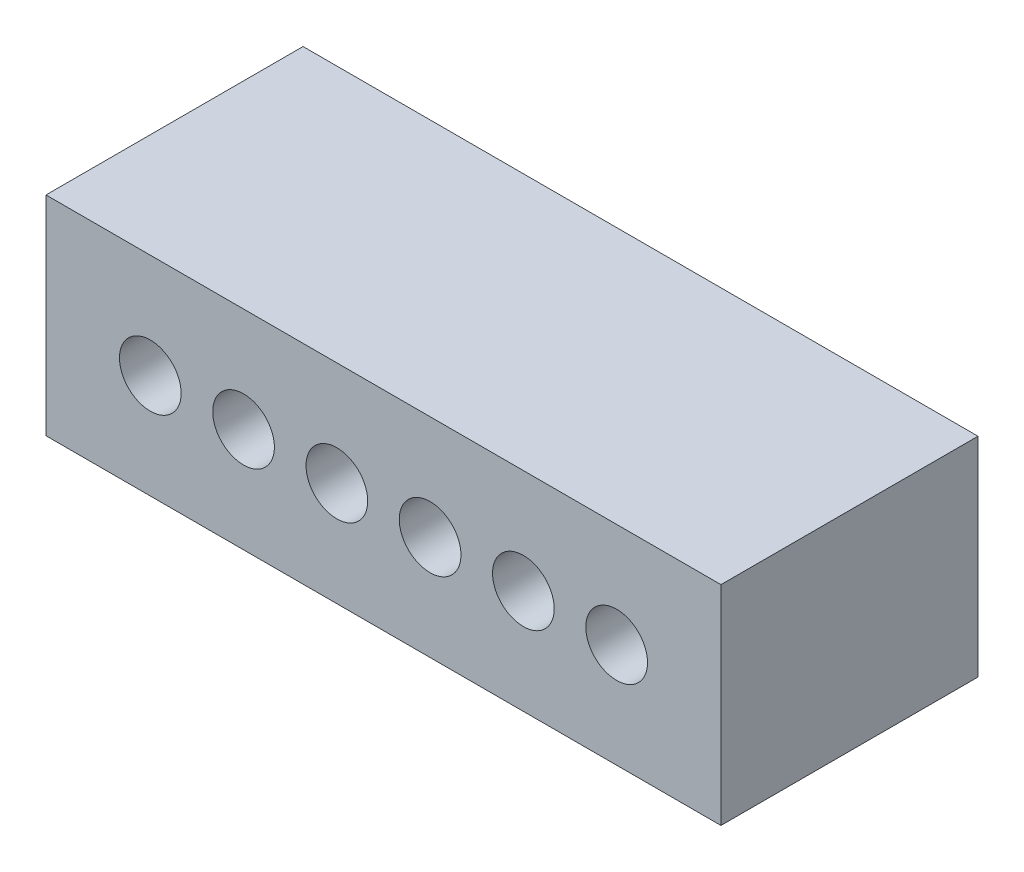
SolidWorks part; units mm, degrees
ref_plane "Front Plane" through (0, 0, 0) normal (0, 0, 1) x (1, 0, 0)
ref_plane "Top Plane" through (0, 0, 0) normal (0, 1, 0) x (1, 0, 0)
ref_plane "Right Plane" through (0, 0, 0) normal (1, 0, 0) x (0, 0, -1)
sketch "Sketch1" plane through (0, 0, 0) normal (0, 0, 1) x (1, 0, 0)
  line L0 (-1.27, 0) -> (1.27, 0) construction
  line L1 (-9.19, -2.84) -> (9.19, -2.84)
  line L2 (-9.19, -2.84) -> (-9.19, 2.84)
  line L3 (-9.19, 2.84) -> (9.19, 2.84)
  line L4 (9.19, -2.84) -> (9.19, 2.84)
  line L5 (-9.19, -2.84) -> (9.19, 2.84) construction
  line L6 (-9.19, 2.84) -> (9.19, -2.84) construction
  circle A0 centre (-6.35, 0) radius 0.84
  circle A6 centre (-3.81, 0) radius 0.84
  circle A7 centre (-1.27, 0) radius 0.84
  circle A8 centre (1.27, 0) radius 0.84
  circle A9 centre (3.81, 0) radius 0.84
  circle A10 centre (6.35, 0) radius 0.84
  point P0 (0, 0)
  point P18 (0, 0)
  dimension "D1" = 1.68
  dimension "D4" = 2
  dimension "D5" = 2
  dimension "D3" = 2.54
  dimension "D2" = 6
extrude "Boss-Extrude1" add sketch "Sketch1" along normal blind 7
